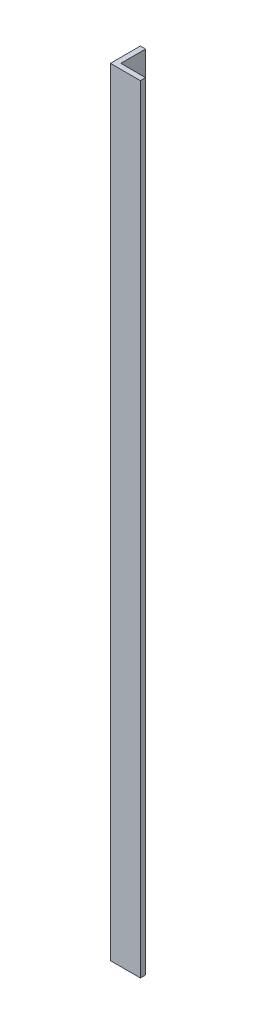
SolidWorks part; units mm, degrees
ref_plane "Front Plane" through (0, 0, 0) normal (0, 0, 1) x (1, 0, 0)
ref_plane "Top Plane" through (0, 0, 0) normal (0, 1, 0) x (1, 0, 0)
ref_plane "Right Plane" through (0, 0, 0) normal (1, 0, 0) x (0, 0, -1)
sketch "Sketch1" plane through (0, 0, 0) normal (0, 1, 0) x (1, 0, 0)
  line L0 (0, 0) -> (0, 19.31)
  line L1 (0, 19.31) -> (3.35, 19.31)
  line L2 (3.35, 19.31) -> (3.35, 3.35)
  line L3 (3.35, 3.35) -> (19.31, 3.35)
  line L4 (19.31, 3.35) -> (19.31, 0)
  line L5 (19.31, 0) -> (0, 0)
  dimension "D1" = 19.31
  dimension "D2" = 3.35
extrude "Boss-Extrude1" add sketch "Sketch1" along normal blind 500
equation "\"8mm hole\" = 8.4mm'used to be the diameter of the linear motion rods"
equation "\"22mm hole\"= 23mm'this is the size of the hole for the nema 17 standard was 22mm"
equation "\"15mm hole\"= 15.8mm'this is the hole for the linear motion sliders, they are all set to this measurement so if you have different sized bearing sliders you may have to adjust individually"
equation "\"bed height offset\"= 3mm'this is how far the bed has been offset from a low point (probably don't want to edit, but can)"
equation "\"#10 nut width\"= 9.6mm'this is the width of a nut from flat side to other flat side"
equation "\"#10 bolt diameter\"= 5mm'This is the diameter including the threads"
equation "\"Al_width\"= 19.31mm'Self explainatory"
equation "\"Al_thick\"= 3.35mm"
equation "\"lin_rd_vert_hole_tol\"= 0.5mm"
equation "\"lin_rd_horz_hole_tol\"= 0.5mm"
equation "\"lin_rd_diam\"= 8mm"
equation "\"slid_diam\"= 15mm"
equation "\"slid_vert_tol\"= 0.7mm"
equation "\"mot_face_ridge_diam\"= 22mm"
equation "\"mot_face_ridge_tol\"= 1mm"
equation "\"slid_horz_tol\"= 0.8"
equation "\"D1@Sketch1\"= \"Al_width\""
equation "\"Al_thick_tol\" = 0.45mm"
equation "\"Al_width_tol\" = 0.7mm"
